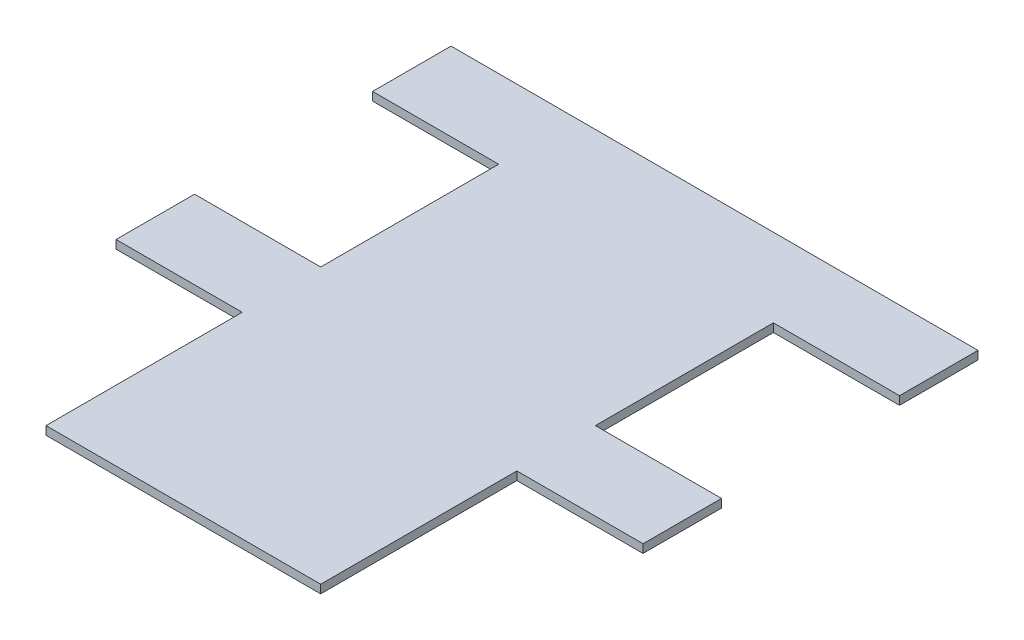
SolidWorks part; units mm, degrees
ref_plane "Front Plane" through (0, 0, 0) normal (0, 0, 1) x (1, 0, 0)
ref_plane "Top Plane" through (0, 0, 0) normal (0, 1, 0) x (1, 0, 0)
ref_plane "Right Plane" through (0, 0, 0) normal (1, 0, 0) x (0, 0, -1)
sketch "Sketch2" plane through (0, 0, 0) normal (0, 1, 0) x (1, 0, 0)
  line L0 (-22.5, 94.75) -> (-22.5, 80.75)
  line L1 (-22.5, 80.75) -> (0, 80.75)
  line L2 (0, 80.75) -> (0, 49)
  line L3 (0, 49) -> (-22.5, 49)
  line L4 (-22.5, 49) -> (-22.5, 35)
  line L5 (-22.5, 35) -> (0, 35)
  line L6 (0, 35) -> (0, 0)
  line L8 (49, 0) -> (49, 35)
  line L9 (49, 35) -> (71.5, 35)
  line L10 (71.5, 35) -> (71.5, 49)
  line L11 (71.5, 49) -> (49, 49)
  line L12 (49, 49) -> (49, 80.75)
  line L13 (49, 80.75) -> (71.5, 80.75)
  line L14 (71.5, 80.75) -> (71.5, 94.75)
  line L15 (71.5, 94.75) -> (-22.5, 94.75)
  line L17 (0, 0) -> (49, 0)
  dimension "D1" = 14
  dimension "D2" = 31.75
  dimension "D3" = 14
  dimension "D4" = 94.75
  dimension "D5" = 94
  dimension "D6" = 49
extrude "Boss-Extrude1" add sketch "Sketch2" along normal blind 1.5
